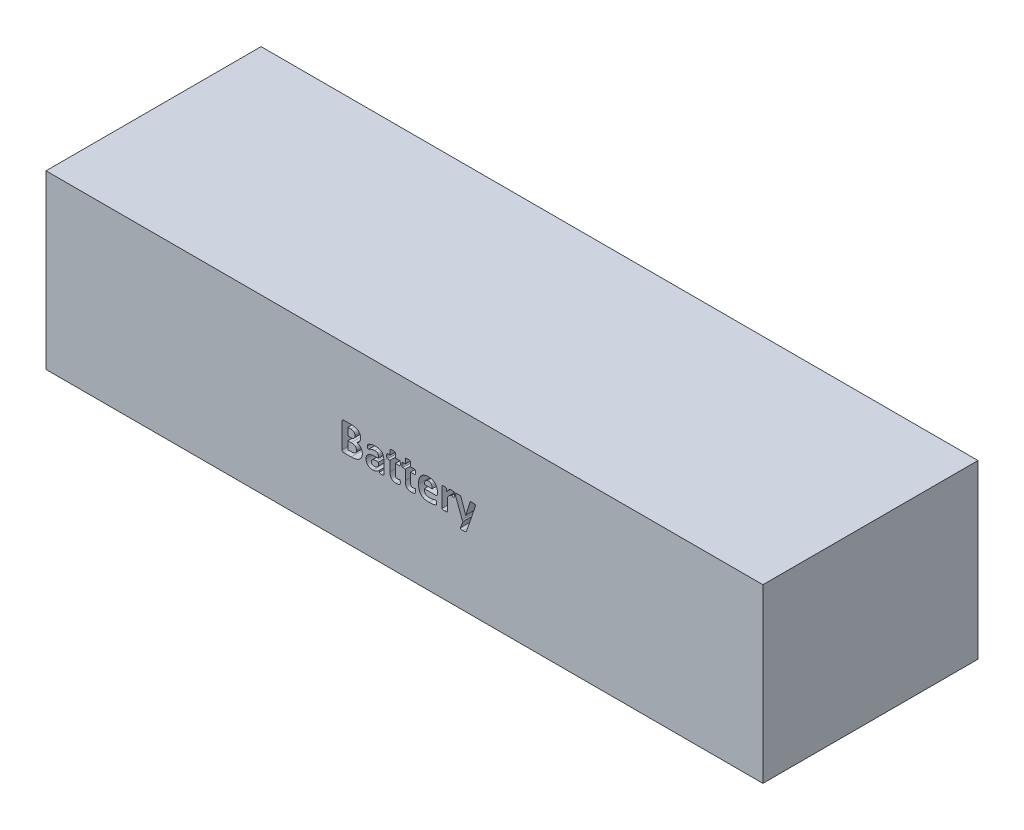
SolidWorks part; units mm, degrees
ref_plane "Front Plane" through (0, 0, 0) normal (0, 0, 1) x (1, 0, 0)
ref_plane "Top Plane" through (0, 0, 0) normal (0, 1, 0) x (1, 0, 0)
ref_plane "Right Plane" through (0, 0, 0) normal (1, 0, 0) x (0, 0, -1)
sketch "Sketch1" plane through (0, 0, 0) normal (0, 0, 1) x (1, 0, 0)
  line L0 (-250, 60) -> (250, 60)
  line L1 (250, 60) -> (250, -60)
  line L2 (-250, 60) -> (-250, -60)
  line L3 (-250, 0) -> (250, 0) construction
  line L4 (-250, -60) -> (250, -60)
  point P2 (0, 60)
  dimension "D1" = 500
  dimension "D2" = 60
extrude "Boss-Extrude1" add sketch "Sketch1" along normal blind 150
sketch "Sketch2" plane through (0, 0, 150) normal (0, 0, 1) x (1, 0, 0)
  text T0 "Battery" font "Calibri" height in points 72
extrude "Cut-Extrude1" cut sketch "Sketch2" against normal blind 10
